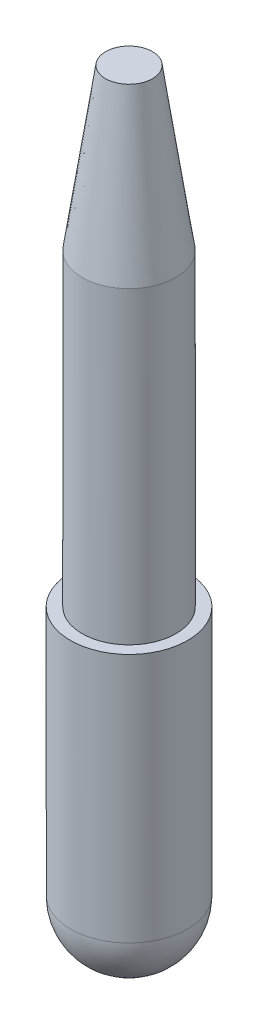
SolidWorks part; units mm, degrees
material "Rubber"
ref_plane "Front" through (0, 0, 0) normal (0, 0, 1) x (1, 0, 0)
ref_plane "Top" through (0, 0, 0) normal (0, 1, 0) x (1, 0, 0)
ref_plane "Right" through (0, 0, 0) normal (1, 0, 0) x (0, 0, -1)
sketch "Sketch1" plane through (0, 0, 0) normal (0, 1, 0) x (1, 0, 0)
  circle A0 centre (0, 0) radius 3.8
extrude "Extrude1" add sketch "Sketch1" along normal blind 25
sketch "Sketch2" plane through (0, 0, 0) normal (0, -1, 0) x (1, 0, 0)
  circle A0 centre (0, 0) radius 4.75
extrude "Extrude2" add sketch "Sketch2" along normal blind 20.25
sketch "Sketch3" plane through (0, 0, 0) normal (1, 0, 0) x (0, 0, -1)
  line L0 (-4.75, -20.25) -> (4.75, -20.25) construction
  line L1 (0, -25) -> (0, -20.25)
  line L2 (0, -20.25) -> (-4.75, -20.25)
  line L3 (0, -25.5191) -> (0, -15.9912) construction
  arc A0 (-4.75, -20.25) -> (0, -25) centre (0, -20.25) ccw
revolve "Revolve1" add sketch "Sketch3" angle 360 about L3
sketch "Sketch4" plane through (0, 0, 0) normal (1, 0, 0) x (0, 0, -1)
  line L0 (0, 25) -> (3.8, 25)
  line L1 (3.8, 25) -> (-3.8, 25) construction
  line L2 (3.8, 25) -> (1.9, 38)
  line L3 (1.9, 38) -> (0, 38)
  line L4 (0, 38) -> (0, 25)
  line L5 (0, 39.3919) -> (0, 22.7614) construction
  dimension "D1" = 13
revolve "Revolve2" add sketch "Sketch4" angle 360 about L5
